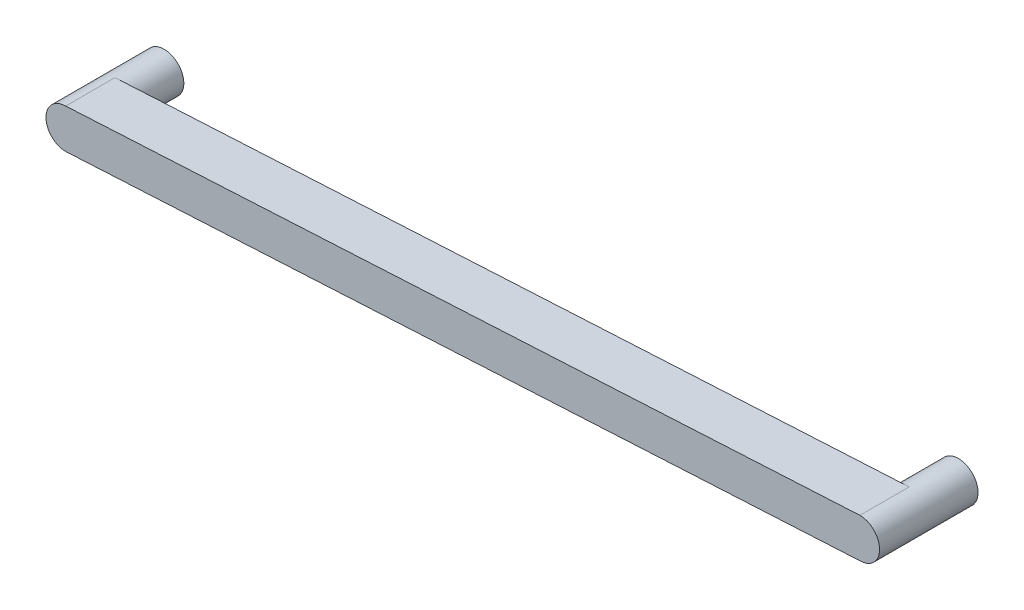
SolidWorks part; units mm, degrees
ref_plane "Alzado" through (0, 0, 0) normal (0, 0, 1) x (1, 0, 0)
ref_plane "Planta" through (0, 0, 0) normal (0, 1, 0) x (1, 0, 0)
ref_plane "Vista lateral" through (0, 0, 0) normal (1, 0, 0) x (0, 0, -1)
sketch "Croquis1" plane through (0, 0, 0) normal (0, 0, 1) x (1, 0, 0)
  line L0 (0, 0) -> (24.2, 0) construction
  line L1 (24.2, 0) -> (24.2, 1.3) construction
  line L2 (24.2, 1.3) -> (0, 0) construction
  line L3 (0, 0.6) -> (24.2, 1.9)
  line L4 (0, -0.6) -> (24.2, 0.7)
  arc A0 (0, 0.6) -> (0, -0.6) centre (0, 0) ccw
  arc A1 (24.2, 0.7) -> (24.2, 1.9) centre (24.2, 1.3) ccw
  dimension "D1" = 24.2
  dimension "D3" = 1.2
  dimension "D4" = 1.2
  dimension "D2" = 1.3
extrude "Saliente-Extruir1" add sketch "Croquis1" along normal blind 1.5
sketch "Croquis2" plane through (0, 0, 0) normal (0, 0, -1) x (-1, 0, 0)
  circle A0 centre (-24.2, 1.3) radius 0.6
  circle A1 centre (0, 0) radius 0.6
  arc A4 (0, -0.6) -> (0, 0.6) centre (0, 0) ccw construction
extrude "Saliente-Extruir2" add sketch "Croquis2" along normal blind 1.5
